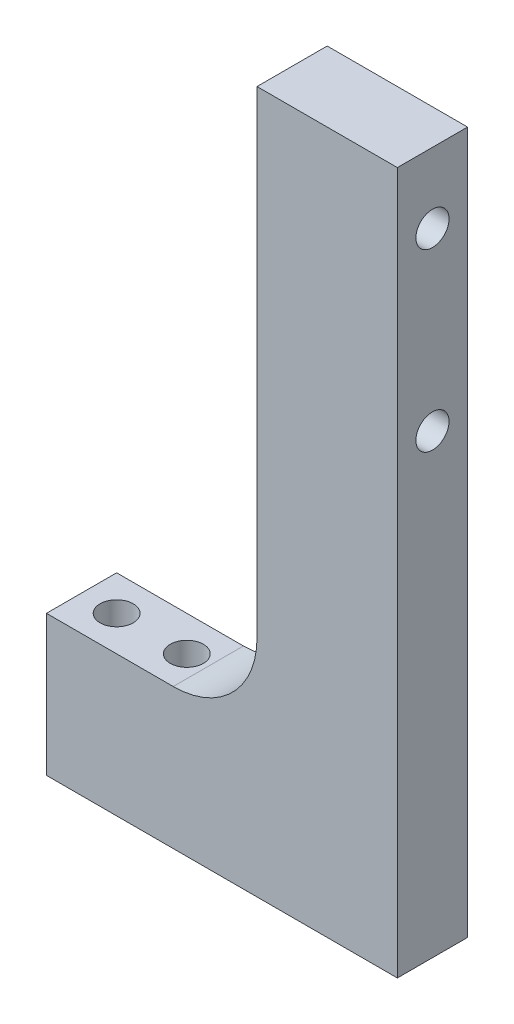
SolidWorks part; units mm, degrees
ref_plane "Front Plane" through (0, 0, 0) normal (0, 0, 1) x (1, 0, 0)
ref_plane "Top Plane" through (0, 0, 0) normal (0, 1, 0) x (1, 0, 0)
ref_plane "Right Plane" through (0, 0, 0) normal (1, 0, 0) x (0, 0, -1)
sketch "Sketch1" plane through (0, 0, 0) normal (0, 0, 1) x (1, 0, 0)
  line L0 (0, 194.7318) -> (0, -59.2682)
  line L1 (0, -59.2682) -> (-127, -59.2682)
  line L2 (-127, -59.2682) -> (-127, -8.4682)
  line L3 (-127, -8.4682) -> (-50.8, -8.4682)
  line L4 (-50.8, -8.4682) -> (-50.8, 194.7318)
  line L5 (-50.8, 194.7318) -> (0, 194.7318)
  dimension "D1" = 254
  dimension "D2" = 127
  dimension "D3" = 50.8
  dimension "D4" = 50.8
extrude "Boss-Extrude1" add sketch "Sketch1" along normal blind 25.4
sketch "Sketch2" plane through (-50.8, 0, 0) normal (-1, 0, 0) x (0, 0, 1)
  line L0 (25.4, 194.7318) -> (0, 194.7318) construction
  line L1 (0, 194.7318) -> (25.4, 194.7318)
  line L2 (0, 194.7318) -> (0, -8.4682)
  line L3 (0, -8.4682) -> (25.4, -8.4682)
  line L4 (25.4, 194.7318) -> (25.4, -8.4682)
  line L5 (0, 194.7318) -> (25.4, -8.4682) construction
  line L6 (0, -8.4682) -> (25.4, 194.7318) construction
  line L7 (0, 194.7318) -> (0, -8.4682) construction
  circle A0 centre (12.7, 105.8318) radius 2.54
  circle A1 centre (12.7, 169.3318) radius 2.54
  point P0 (12.7, 93.1318)
  dimension "D1" = 25.4
  dimension "D2" = 63.5
sketch "Sketch3" plane through (0, -8.4682, 0) normal (0, 1, 0) x (1, 0, 0)
  line L0 (-127, -25.4) -> (-127, 0) construction
  line L1 (-50.8, 0) -> (-127, 0) construction
  circle A0 centre (-114.3, -12.7) radius 2.54
  circle A1 centre (-88.9, -12.7) radius 2.54
  dimension "D1" = 12.7
  dimension "D2" = 25.4
  dimension "D3" = 12.7
  dimension "D4" = 12.7
hole_wizard "M10 Clearance Hole1" positions "Sketch4" profile "Sketch5" hole size "M10" standard "ANSI Metric" end condition through all
sketch "Sketch4" plane through (0, -8.4682, 0) normal (0, 1, 0) x (1, 0, 0)
  point P0 (-114.3, -12.7)
  point P3 (-88.9, -12.7)
sketch "Sketch5" plane through (-114.3, -8.4682, 12.7) normal (1, 0, 0) x (0, 0, 1)
  line L0 (0, 0) -> (0, 50.8)
  line L1 (0, 50.8) -> (6, 50.8)
  line L2 (6, 50.8) -> (6, 0)
  line L5 (6, 0) -> (0, 0)
  line L11 (0, -6.35) -> (0, 107.95) construction
  dimension "Thru Hole Dia." = 12
  dimension "Thru Hole Depth" = 50.8
hole_wizard "M10 Clearance Hole2" positions "Sketch6" profile "Sketch7" hole size "M10" standard "ANSI Metric" end condition through all
sketch "Sketch6" plane through (-50.8, 0, 0) normal (-1, 0, 0) x (0, 0, 1)
  point P0 (12.7, 169.3318)
  point P3 (12.7, 105.8318)
sketch "Sketch7" plane through (-50.8, 169.3318, 12.7) normal (0, 1, 0) x (0, 0, 1)
  line L0 (0, 0) -> (0, 50.8)
  line L1 (0, 50.8) -> (6, 50.8)
  line L2 (6, 50.8) -> (6, 0)
  line L5 (6, 0) -> (0, 0)
  line L11 (0, -6.35) -> (0, 107.95) construction
  dimension "Thru Hole Dia." = 12
  dimension "Thru Hole Depth" = 50.8
fillet "Fillet1" radius 30.32 1 edges at (-50.8, -8.4682, 12.7)
